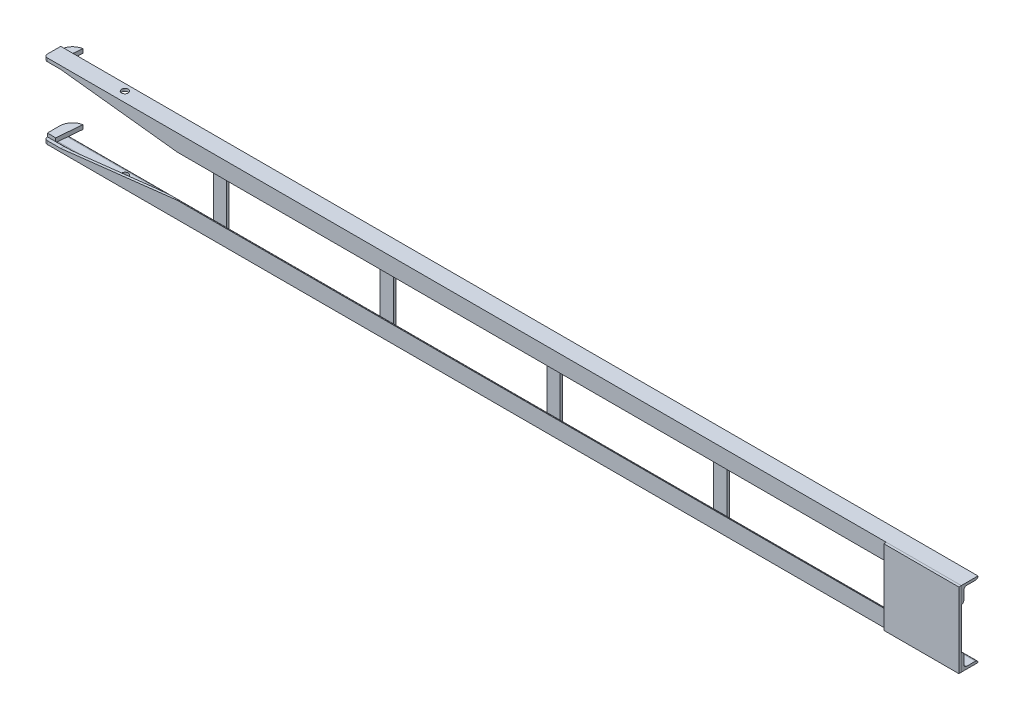
SolidWorks part; units mm, degrees
ref_plane "Front Plane" through (0, 0, 0) normal (0, 0, 1) x (1, 0, 0)
ref_plane "Top Plane" through (0, 0, 0) normal (0, 1, 0) x (1, 0, 0)
ref_plane "Right Plane" through (0, 0, 0) normal (1, 0, 0) x (0, 0, -1)
sketch "Sketch1" plane through (0, 0, 0) normal (0, 0, 1) x (1, 0, 0)
  line L0 (0, 0) -> (1100, 0)
  line L1 (0, -90) -> (1100, -90)
  dimension "D1" = 1100
  dimension "D2" = 90
other "L angle (equal) 20X20X3(6)"
ref_plane "Plane1" through (0, 0, 0) normal (1, 0, 0) x (0, -1, 0)
sketch "Sketch17" plane through (0, 0, 0) normal (1, 0, 0) x (0, -1, 0)
  line L0 (0, 20) -> (0, 0)
  line L2 (3, 17) -> (3, 6.5)
  line L3 (6.5, 3) -> (17, 3)
  line L5 (20, 0) -> (0, 0)
  arc A0 (3, 17) -> (0, 20) centre (0, 17) ccw
  arc A1 (20, 0) -> (17, 3) centre (17, 0) ccw
  arc A2 (6.5, 3) -> (3, 6.5) centre (6.5, 6.5) cw
  point P8 (0, 10)
  point P9 (10, 0)
  point P10 (0, 0)
  dimension "Radius_2" = 3
  dimension "Radius_1" = 3.5
  dimension "V_leg" = 20
  dimension "H_leg" = 20
  dimension "thickness" = 3
other "L angle (equal) 20X20X3(7)"
ref_plane "Plane2" through (0, -90, 0) normal (-1, 0, 0) x (0, 1, 0)
sketch "Sketch19" plane through (0, -90, 0) normal (-1, 0, 0) x (0, 1, 0)
  line L0 (0, 20) -> (0, 0)
  line L2 (3, 17) -> (3, 6.5)
  line L3 (6.5, 3) -> (17, 3)
  line L5 (20, 0) -> (0, 0)
  arc A0 (3, 17) -> (0, 20) centre (0, 17) ccw
  arc A1 (20, 0) -> (17, 3) centre (17, 0) ccw
  arc A2 (6.5, 3) -> (3, 6.5) centre (6.5, 6.5) cw
  point P8 (0, 10)
  point P9 (10, 0)
  point P10 (0, 0)
  dimension "Radius_2" = 3
  dimension "Radius_1" = 3.5
  dimension "V_leg" = 20
  dimension "H_leg" = 20
  dimension "thickness" = 3
sketch "Sketch16" plane through (0, -90, 0) normal (0, -1, 0) x (1, 0, 0)
  line L0 (0, -20) -> (0, 0) construction
  line L1 (1100, 0) -> (0, 0) construction
  circle A0 centre (85, -12) radius 4
  dimension "D1" = 8
  dimension "D2" = 85
  dimension "D3" = 12
extrude "Cut-Extrude1" cut sketch "Sketch16" against normal through all
sketch "Sketch18" plane through (0, 0, 0) normal (0, 0, 1) x (1, 0, 0)
  line L1 (1100, 0) -> (0, 0) construction
  line L20 (1100, -90) -> (1010, -90)
  line L21 (1100, -90) -> (1100, 0)
  line L22 (1100, 0) -> (1010, 0)
  line L23 (1010, -90) -> (1010, 0)
  dimension "D6" = 90
extrude "Boss-Extrude1" add sketch "Sketch18" along normal blind 3 separate body
sketch "Sketch20" plane through (0, 0, 0) normal (0, 0, 1) x (1, 0, 0)
  line L0 (0, -86) -> (20, -86)
  line L1 (0, -90) -> (0, -70) construction
  line L2 (20, -86) -> (160, -70)
  line L3 (1100, -70) -> (0, -70) construction
  line L4 (0, -86) -> (0, -70)
  line L5 (1100, -90) -> (0, -90) construction
  line L6 (0, -70) -> (160, -70)
  line L7 (0, -20) -> (160, -20)
  line L8 (0, -4) -> (0, -20)
  line L10 (20, -4) -> (160, -20)
  line L11 (0, -4) -> (20, -4)
  dimension "D1" = 4
  dimension "D2" = 20
  dimension "D3" = 160
extrude "Cut-Extrude2" cut sketch "Sketch20" against normal blind 4
sketch "Sketch21" plane through (0, -3, 0) normal (0, -1, 0) x (1, 0, 0)
  line L0 (0, -20) -> (0, 0) construction
  line L1 (0, -4) -> (10, -4)
  line L2 (0, -4) -> (0, -20)
  line L3 (10, -4) -> (12.6247, -34)
  line L5 (1100, 0) -> (0, 0) construction
  spline S0 degree 2 poles (12.6247, -34) (1.7589, -31.5343) (0, -20) knots 0 0 0 1 1 1
  dimension "D1" = 4
  dimension "D2" = 10
  dimension "D3" = 12.6247
  dimension "D5" = 30
extrude "Boss-Extrude2" add sketch "Sketch21" along normal blind 5 separate body
sketch "Sketch22" plane through (0, -87, 0) normal (0, 1, 0) x (1, 0, 0)
  line L3 (0, 20) -> (0, 4)
  line L4 (0, 4) -> (10, 4)
  line L5 (10, 4) -> (12.6247, 34)
  line L6 (0, 20) -> (0, 4)
  line L7 (0, 4) -> (10, 4)
  line L8 (10, 4) -> (12.6247, 34)
  parabola Q1 (12.6247, 34) -> (0, 20) focus (9.3923, 24.8974) apex (4.5058, 29.7633)
  parabola Q2 (12.6247, 34) -> (0, 20) focus (9.3923, 24.8974) apex (4.5058, 29.7633)
  dimension "D1" = 0
extrude "Boss-Extrude3" add sketch "Sketch22" along normal blind 5 separate body
fillet "Fillet1" radius 4 1 edges at (0, -88, 0)
fillet "Fillet2" radius 4 1 edges at (0, -2, 0)
sketch "Sketch23" plane through (0, 0, -3) normal (0, 0, -1) x (-1, 0, 0)
  line L0 (-1100, -90) -> (0, -90) construction
  line L1 (-1100, 0) -> (0, 0) construction
  line L2 (-400, -10) -> (-416, -10)
  line L3 (-416, -10) -> (-416, -80)
  line L4 (-416, -80) -> (-400, -80)
  line L5 (-400, -80) -> (-400, -10)
  line L6 (-600, -10) -> (-616, -10)
  line L7 (-616, -10) -> (-616, -80)
  line L8 (-200, -10) -> (-216, -10)
  line L9 (-216, -10) -> (-216, -80)
  line L10 (-216, -80) -> (-200, -80)
  line L11 (-200, -80) -> (-200, -10)
  line L12 (-616, -80) -> (-600, -80)
  line L13 (-600, -80) -> (-600, -10)
  line L14 (-800, -10) -> (-816, -10)
  line L15 (-816, -10) -> (-816, -80)
  line L16 (-816, -80) -> (-800, -80)
  line L17 (-800, -80) -> (-800, -10)
  line L22 (-1000, -10) -> (-1016, -10) [skipped]
  line L23 (-1016, -10) -> (-1016, -80) [skipped]
  line L24 (-1016, -80) -> (-1000, -80) [skipped]
  line L25 (-1000, -80) -> (-1000, -10) [skipped]
  dimension "D1" = 10
  dimension "D2" = 10
  dimension "D3" = 5
extrude "Boss-Extrude4" add sketch "Sketch23" along normal blind 3 separate body
